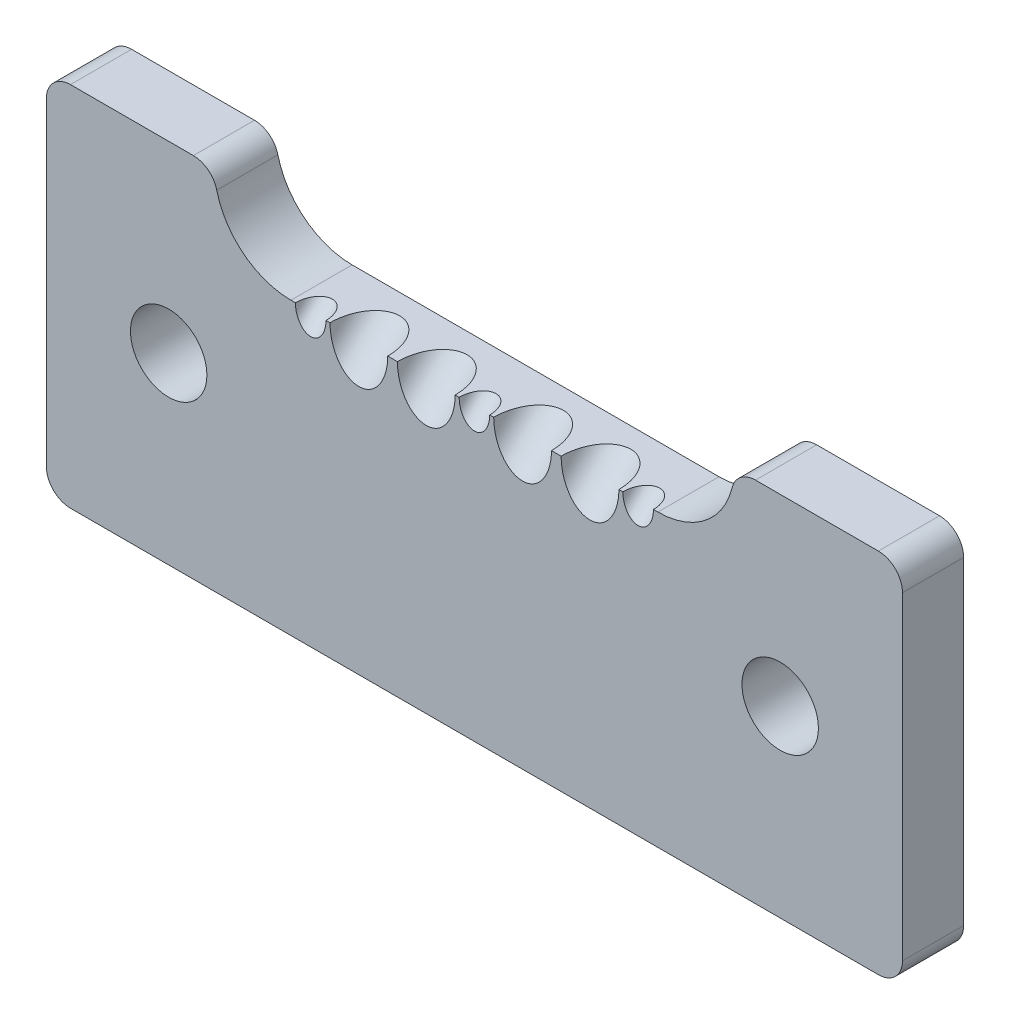
SolidWorks part; units mm, degrees
ref_plane "Front Plane" through (0, 0, 0) normal (0, 0, 1) x (1, 0, 0)
ref_plane "Top Plane" through (0, 0, 0) normal (0, 1, 0) x (1, 0, 0)
ref_plane "Right Plane" through (0, 0, 0) normal (1, 0, 0) x (0, 0, -1)
sketch "Sketch1" plane through (0, 0, 0) normal (0, 0, 1) x (1, 0, 0)
  line L0 (25.4, 38.1) -> (63.5, 38.1) construction
  line L1 (2.5, 0) -> (86.4, 0)
  line L2 (0, 2.5) -> (0, 35.6)
  line L3 (2.5, 38.1) -> (15.2637, 38.1)
  line L4 (88.9, 2.5) -> (88.9, 35.6)
  line L5 (0, 0) -> (88.9, 38.1) construction
  line L6 (0, 38.1) -> (88.9, 0) construction
  line L8 (25.4, 30.16) -> (63.5, 30.16)
  line L9 (73.6363, 38.1) -> (86.4, 38.1)
  line L10 (17.46, 38.1) -> (25.4, 38.1) construction
  line L11 (25.4, 38.1) -> (17.46, 38.1)
  line L12 (63.5, 38.1) -> (71.44, 38.1) construction
  line L13 (63.5, 38.1) -> (71.44, 38.1)
  circle A0 centre (12.7, 19.05) radius 3.9688
  circle A1 centre (76.2, 19.05) radius 3.9687
  arc A2 (17.691, 36.1987) -> (25.4, 30.16) centre (25.4, 38.1) ccw
  arc A3 (63.5, 30.16) -> (71.209, 36.1987) centre (63.5, 38.1) ccw
  arc A4 (2.5, 38.1) -> (0, 35.6) centre (2.5, 35.6) ccw
  arc A5 (0, 2.5) -> (2.5, 0) centre (2.5, 2.5) ccw
  arc A6 (86.4, 0) -> (88.9, 2.5) centre (86.4, 2.5) ccw
  arc A7 (88.9, 35.6) -> (86.4, 38.1) centre (86.4, 35.6) ccw
  arc A8 (73.6363, 38.1) -> (71.209, 36.1987) centre (73.6363, 35.6) ccw
  arc A9 (17.691, 36.1987) -> (15.2637, 38.1) centre (15.2637, 35.6) ccw
  point P4 (44.45, 19.05)
  point P10 (44.45, 38.1)
  point P13 (0, 0)
  point P14 (0, 0)
  point P17 (0, 0)
  point P18 (0, 0)
  point P20 (0, 0)
  dimension "D3" = 7.9375
  dimension "D7" = 7.94
  dimension "D8" = 2.5
  dimension "D1" = 38.1
  dimension "D2" = 88.9
  dimension "D4" = 12.7
  dimension "D5" = 12.7
  dimension "D6" = 38.1
extrude "Boss-Extrude1" add sketch "Sketch1" along normal blind 6.35 contours A2 A9 L3 A4 L2 A5 L1 A6 L4 A7 L9 A8 A3 L8 A0 A1
ref_plane "Plane1" through (0, 11.905, -11.905) normal (0, -0.7071, 0.7071) x (1, 0, 0)
sketch "Sketch2" plane through (0, 11.905, -11.905) normal (0, -0.7071, 0.7071) x (1, 0, 0)
  line L0 (25.4, 25.8165) -> (63.5, 25.8165) construction
  circle A0 centre (49.45, 25.8165) radius 3
  circle A1 centre (39.45, 25.8165) radius 3
  circle A2 centre (32.45, 25.8165) radius 3
  circle A3 centre (56.45, 25.8165) radius 3
  circle A4 centre (61.45, 25.8165) radius 1.5875
  circle A5 centre (27.45, 25.8165) radius 1.5875
  circle A6 centre (44.45, 25.8165) radius 1.5875
  point P10 (44.45, 25.8165)
  dimension "D1" = 6
  dimension "D6" = 3.175
  dimension "D7" = 5
  dimension "D2" = 7
  dimension "D3" = 7
  dimension "D4" = 5
  dimension "D5" = 5
  dimension "D8" = 5
extrude "Cut-Extrude1" cut sketch "Sketch2" against normal through all both and the other way through all
sketch "Sketch3" plane through (0, 0, 6.35) normal (0, 0, 1) x (1, 0, 0)
  line L0 (0, 2.5) -> (0, 35.6) construction
  circle A0 centre (76.2, 19.05) radius 3.9687 construction
  circle A1 centre (12.7, 19.05) radius 3.9688 construction
  circle A2 centre (76.2, 19.05) radius 3.9687 construction
  circle A3 centre (12.7, 19.05) radius 3.9688 construction
  circle A4 centre (12.7, 19.05) radius 12.7 construction
  circle A5 centre (76.2, 19.05) radius 12.7 construction
